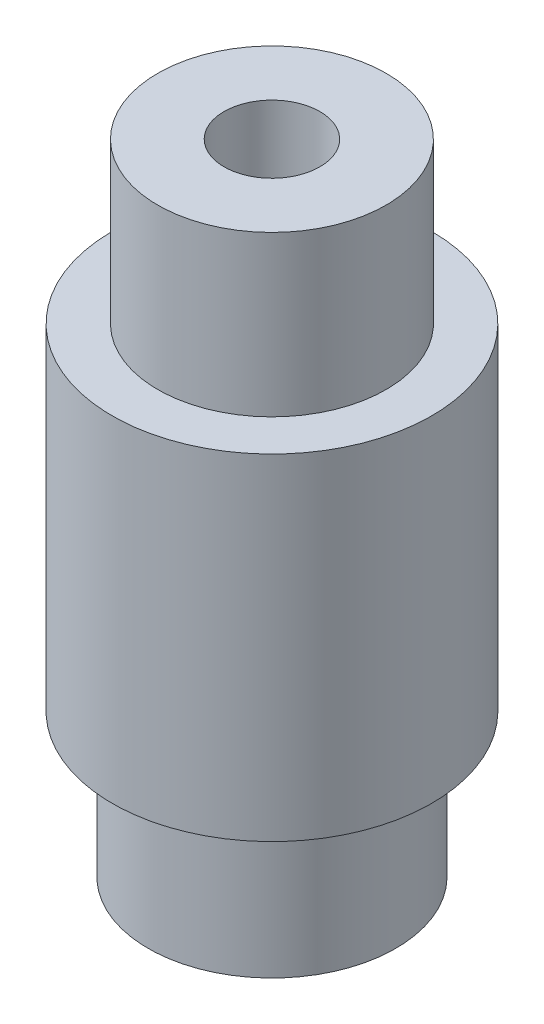
SolidWorks part; units mm, degrees
ref_plane "Спереди" through (0, 0, 0) normal (0, 0, 1) x (1, 0, 0)
ref_plane "Сверху" through (0, 0, 0) normal (0, 1, 0) x (1, 0, 0)
ref_plane "Справа" through (0, 0, 0) normal (1, 0, 0) x (0, 0, -1)
sketch "Эскиз1" plane through (0, 0, 0) normal (0, 0, 1) x (1, 0, 0)
  line L0 (-3, 0) -> (-7.75, 0)
  line L1 (-7.75, 0) -> (-7.75, 8.9879)
  line L2 (-7.75, 8.9879) -> (-10, 8.9879)
  line L3 (-10, 8.9879) -> (-10, 30)
  line L7 (-3, 40) -> (-3, 0)
  line L8 (0, -8.7284) -> (0, 48.8805) construction
  line L9 (-10, 30) -> (-7.15, 30)
  line L10 (-7.15, 30) -> (-7.15, 40)
  line L11 (-7.15, 40) -> (-3, 40)
  point P3 (0, 0)
  point P8 (0, 0)
  point P11 (0, 0)
  point P12 (0, 0)
  point P13 (0, 0)
  point P14 (0, 0)
revolve "Повернуть1" add sketch "Эскиз1" angle 360 about L8
